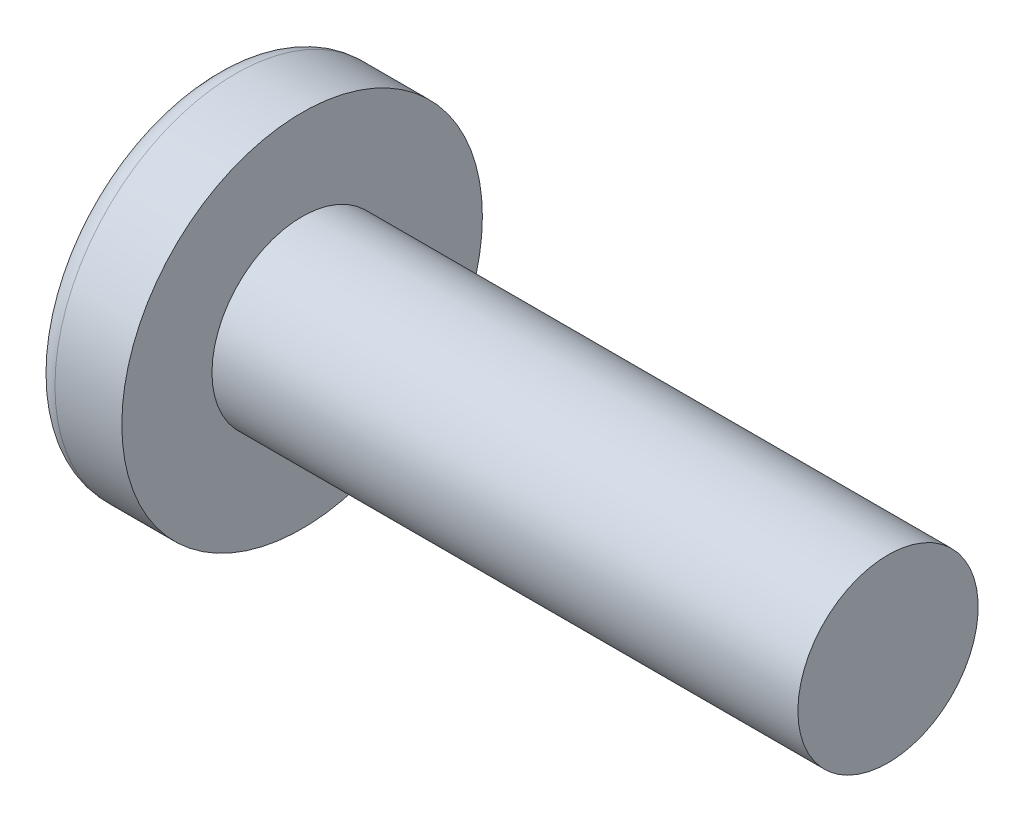
SolidWorks part; units mm, degrees
ref_plane "Plane1" through (0, 0, 0) normal (0, 0, 1) x (1, 0, 0)
ref_plane "Plane2" through (0, 0, 0) normal (0, 1, 0) x (1, 0, 0)
ref_plane "Plane3" through (0, 0, 0) normal (1, 0, 0) x (0, 0, -1)
sketch "BodySke" plane through (0, 0, 0) normal (0, 0, 1) x (1, 0, 0)
  line L0 (3.1, 2) -> (3.1, 4)
  line L1 (3.8, 6.35) -> (3.8, -3.175) construction
  line L2 (-25.4, 0) -> (127, 0) construction
  line L3 (16.1, 0) -> (0, 0)
  line L4 (3.1, 2) -> (16.1, 2)
  line L5 (16.1, 2) -> (16.1, 0)
  line L6 (1.6164, 4) -> (3.1, 4)
  line L7 (3.1, -2) -> (16.1, -2) construction
  line L8 (3.1, 6.35) -> (3.1, -3.175) construction
  arc A0 (1.227, 3.8007) -> (0, 0) centre (6.5, 0) ccw
  arc A2 (1.227, 3.8007) -> (1.6164, 4) centre (1.6164, 3.52) cw
  dimension "Head_crown_rad" = 6.5
  dimension "Head_fillet_rad" = 0.48
  dimension "Diameter" = 4
  dimension "Length" = 13
  dimension "Head_ht" = 3.1
  dimension "Head_dia" = 8
  dimension "Advance" = 0.7
  dimension "Thread_nom" = 13
revolve "Base-Revolve" add sketch "BodySke" angle 360 about L2
cosmetic thread "ThreadCosmetic" [suppressed] parameters "Thread_length"=12.3, "Thread_minor"=3.22
sketch "Sketch3" plane through (0, 0, 0) normal (1, 0, 0) x (0, 0, -1)
  line L0 (0.465, -2.2) -> (-0.465, -2.2)
  line L1 (0.465, -2.2) -> (0.465, 2.2)
  line L2 (-0.465, 2.2) -> (0.465, 2.2)
  line L3 (-0.465, 2.2) -> (-0.465, -2.2)
  dimension "Cross_dia" = 4.4
  dimension "D1" = 2.2
  dimension "Cross_width" = 0.93
  dimension "D2" = 0.465
ref_plane "Plane4" through (2.45, 0, 0) normal (1, 0, 0) x (0, 0, -1)
sketch "Sketch4" plane through (2.45, 0, 0) normal (1, 0, 0) x (0, 0, -1)
  line L0 (0.2325, -0.2325) -> (-0.2325, -0.2325)
  line L1 (0.2325, -0.2325) -> (0.2325, 0.2325)
  line L2 (-0.2325, 0.2325) -> (0.2325, 0.2325)
  line L3 (-0.2325, 0.2325) -> (-0.2325, -0.2325)
  dimension "D2" = 0.465
  dimension "D1" = 0.465
  dimension "D3" = 0.2325
  dimension "D4" = 0.2325
loft "Cut-Loft1" cut profiles "Sketch3", "Sketch4"
pattern_circular "CirPattern1" count 2 every 90 about axis through (0, 0, 0) along (1, 0, 0) of "Cut-Loft1"
sketch "ThdSchSke" plane through (0, 0, 0) normal (0, 0, 1) x (1, 0, 0)
  line L0 (3.8, -1.61) -> (3.5269, -2)
  line L1 (3.8, -1.61) -> (4.0731, -2)
  line L2 (4.0731, -2) -> (4.0731, -2.5)
  line L3 (-3.175, 0) -> (5.1513, 0) construction
  line L5 (4.0731, -2.5) -> (3.5269, -2.5)
  line L6 (3.5269, -2.5) -> (3.5269, -2)
  dimension "Diameter" = 4
  dimension "SideAngle" = 55
  dimension "VeeAngle" = 70
  dimension "Thread_minor" = 3.22
  dimension "Overcut" = 5
  dimension "Start" = 3.8
revolve "ThreadSchematic" [suppressed] cut sketch "ThdSchSke" angle 360 about L3
pattern_linear "ThdSchPat" [suppressed]
equation "\"D1@Sketch3\" = \"Cross_dia@Sketch3\" / 2"
equation "\"D2@Sketch3\" = \"Cross_width@Sketch3\" / 2"
equation "\"D1@Sketch4\" = \"Cross_width@Sketch3\" *.5"
equation "\"D2@Sketch4\" = \"D1@Sketch4\""
equation "\"D3@Sketch4\" = \"D1@Sketch4\" / 2"
equation "\"D4@Sketch4\" = \"D2@Sketch4\" / 2"
equation "\"Thread_length@ThreadCosmetic\" = ((sgn( (\"Length@BodySke\" - \"Advance@BodySke\" ) - \"Thread_nom@BodySke\" )-1)*( (\"Length@BodySke\" - \"Advance@BodySke\" ) - \"Thread_nom@BodySke\" ))/-2+ \"Thread_nom@BodySke\""
equation "\"Thread_minor@ThdSchSke\" = \"Thread_minor@ThreadCosmetic\""
equation "\"Diameter@ThdSchSke\" = \"Diameter@BodySke\""
equation "\"Overcut@ThdSchSke\" = \"Diameter@BodySke\" * 1.25"
equation "\"Start@ThdSchSke\" = \"Head_ht@BodySke\" + \"Length@BodySke\" - \"Thread_length@ThreadCosmetic\"  '---Non-countersunk---"
equation "\"Num_threads@ThdSchPat\" = int( \"Thread_length@ThreadCosmetic\" / \"Advance@BodySke\" + 0.999 )  + 1"
equation "\"Advance@ThdSchPat\" = \"Thread_length@ThreadCosmetic\" /  (\"Num_threads@ThdSchPat\" - 1) 'relax it"
